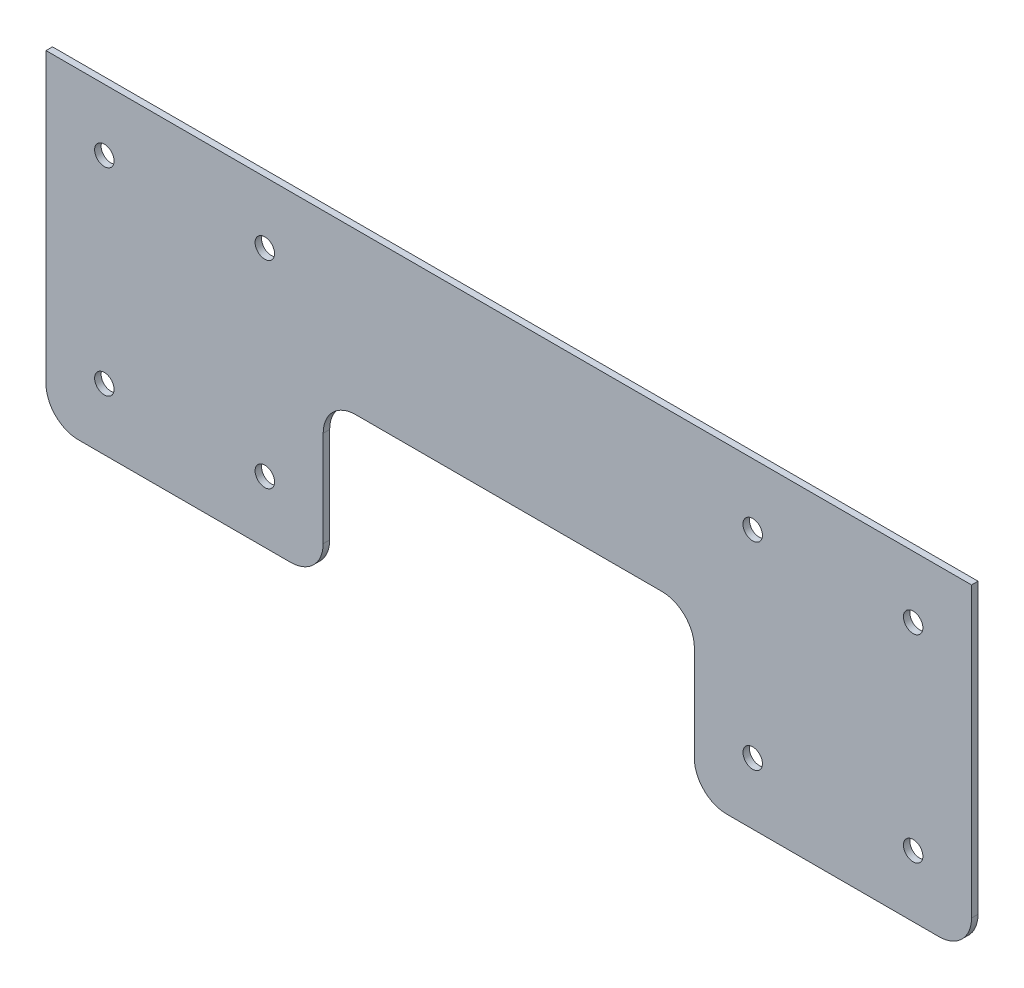
SolidWorks part; units mm, degrees
ref_plane "Front Plane" through (0, 0, 0) normal (0, 0, 1) x (1, 0, 0)
ref_plane "Top Plane" through (0, 0, 0) normal (0, 1, 0) x (1, 0, 0)
ref_plane "Right Plane" through (0, 0, 0) normal (1, 0, 0) x (0, 0, -1)
sketch "Sketch1" plane through (0, 0, 0) normal (0, 0, 1) x (1, 0, 0)
  line L0 (-100, 0) -> (100, 0) construction
  line L1 (100, 30.5) -> (100, -30.5) construction
  line L2 (-100, 30.5) -> (-100, -30.5) construction
  line L3 (0, 65.1273) -> (0, -64.235) construction
  line L4 (-142.75, 49.5) -> (-142.75, -39.5)
  line L5 (-132.75, -49.5) -> (-67.25, -49.5)
  line L6 (-57.25, -39.5) -> (-57.25, -10)
  line L7 (-47.25, 0) -> (47.25, 0)
  line L8 (57.25, -10) -> (57.25, -39.5)
  line L9 (-142.75, 49.5) -> (142.75, 49.5)
  line L10 (142.75, 49.5) -> (142.75, -39.5)
  line L11 (132.75, -49.5) -> (67.25, -49.5)
  circle A0 centre (124.75, 30.5) radius 3
  circle A1 centre (124.75, -30.5) radius 3
  circle A2 centre (75.25, -30.5) radius 3
  circle A3 centre (75.25, 30.5) radius 3
  circle A4 centre (-75.25, -30.5) radius 3
  circle A5 centre (-75.25, 30.5) radius 3
  circle A6 centre (-124.75, 30.5) radius 3
  circle A7 centre (-124.75, -30.5) radius 3
  arc A8 (142.75, -39.5) -> (132.75, -49.5) centre (132.75, -39.5) cw
  arc A9 (57.25, -39.5) -> (67.25, -49.5) centre (67.25, -39.5) ccw
  arc A10 (47.25, 0) -> (57.25, -10) centre (47.25, -10) cw
  arc A11 (-57.25, -10) -> (-47.25, 0) centre (-47.25, -10) cw
  arc A12 (-142.75, -39.5) -> (-132.75, -49.5) centre (-132.75, -39.5) ccw
  arc A13 (-67.25, -49.5) -> (-57.25, -39.5) centre (-67.25, -39.5) ccw
  point P3 (0, 0)
  point P44 (-142.75, -49.5)
  dimension "D2" = 6
  dimension "D3" = 6
  dimension "D15" = 10
  dimension "D1" = 100
  dimension "D4" = 61
  dimension "D5" = 30.5
  dimension "D6" = 24.75
  dimension "D7" = 285.5
  dimension "D8" = 142.75
  dimension "D9" = 99
  dimension "D10" = 49.5
  dimension "D11" = 18
  dimension "D12" = 18
  dimension "D13" = 19
  dimension "D14" = 49.5
extrude "Boss-Extrude1" add sketch "Sketch1" along normal blind 2
